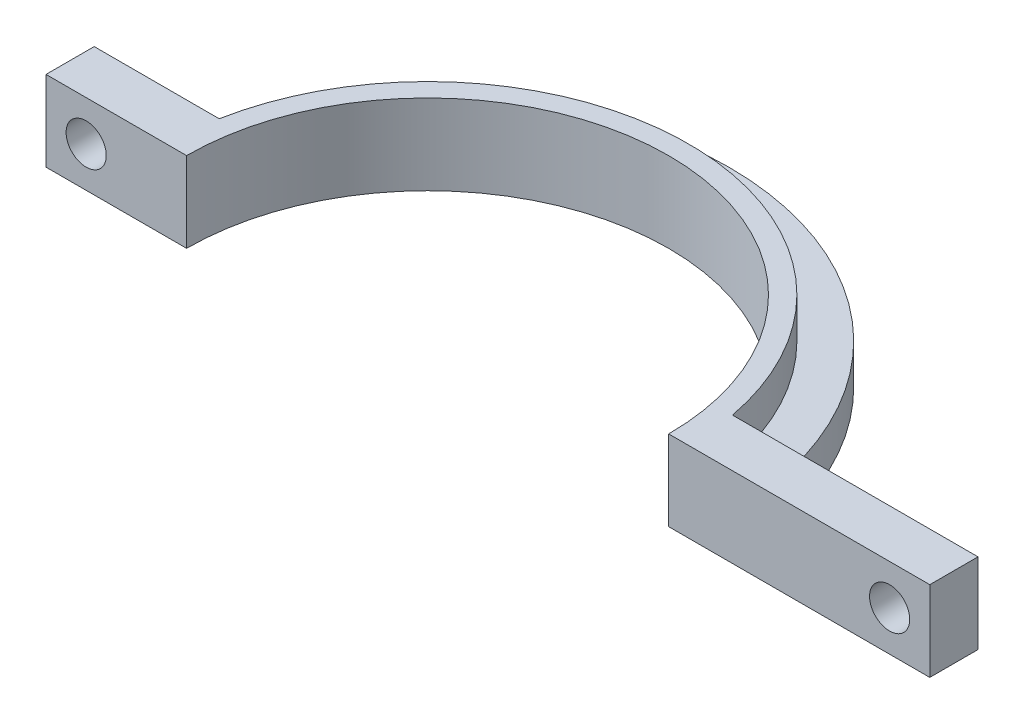
SolidWorks part; units mm, degrees
ref_plane "Front Plane" through (0, 0, 0) normal (0, 0, 1) x (1, 0, 0)
ref_plane "Top Plane" through (0, 0, 0) normal (0, 1, 0) x (1, 0, 0)
ref_plane "Right Plane" through (0, 0, 0) normal (1, 0, 0) x (0, 0, -1)
sketch "Sketch1" plane through (0, 0, 0) normal (0, 1, 0) x (1, 0, 0)
  line L2 (0, 30) -> (0, -30) construction
  line L3 (32.5, 0) -> (62.5, 0)
  line L4 (62.5, 0) -> (62.5, 6)
  line L5 (-32.5, 0) -> (-62.5, 0)
  line L6 (-62.5, 0) -> (-62.5, 6)
  line L7 (62.5, 6) -> (31.9414, 6)
  line L8 (-47.5, 6) -> (-47.5, 0)
  line L11 (-30, 0) -> (-32.5, 0)
  line L12 (30, 0) -> (32.5, 0)
  line L13 (-62.5, 6) -> (-31.9414, 6)
  circle A0 centre (0, 0) radius 30
  circle A3 centre (0, 0) radius 32.5
  dimension "D1" = 60
  dimension "D2" = 65
  dimension "D4" = 6
  dimension "D3" = 30
  dimension "D5" = 15
extrude "Boss-Extrude1" add sketch "Sketch1" along normal blind 10
sketch "Sketch3" plane through (0, 0, 0) normal (0, 0, 1) x (1, 0, 0)
  line L0 (-47.5, 5) -> (-42.5, 5) construction
  line L2 (62.5, 5) -> (57.5, 5) construction
  line L3 (-47.5, 10) -> (-47.5, 0) construction
  line L4 (62.5, 10) -> (62.5, 0) construction
  circle A5 centre (57.5, 5) radius 2.5
  circle A6 centre (-42.5, 5) radius 2.5
  dimension "D1" = 5
  dimension "D2" = 5
extrude "Cut-Extrude1" cut sketch "Sketch3" against normal blind 10
sketch "Sketch5" plane through (0, 0, 0) normal (0, 1, 0) x (1, 0, 0)
  line L0 (-37.5, 0) -> (-32.5, 0)
  line L1 (32.5, 0) -> (37.5, 0)
  circle A0 centre (0, 0) radius 37.5
  circle A1 centre (0, 0) radius 32.5
  dimension "D1" = 75
  dimension "D2" = 65
extrude "Boss-Extrude2" add sketch "Sketch5" along normal blind 5 contours A1 L1 A0 L0
sketch "Sketch9" plane through (0, 0, 0) normal (0, -1, 0) x (1, 0, 0)
  line L0 (-34.8065, -10) -> (-28.2843, -10)
  line L1 (-34.8065, -13.9556) -> (-28.2843, -13.9556)
  line L2 (0, 0) -> (0, -30) construction
  line L5 (-34.8065, -13.9556) -> (-34.8065, -10)
  line L6 (-28.2843, -10) -> (-28.2843, -13.9556)
  line L7 (34.8065, -13.9556) -> (28.2843, -13.9556)
  line L8 (34.8065, -13.9556) -> (34.8065, -10)
  line L9 (34.8065, -10) -> (28.2843, -10)
  line L10 (28.2843, -10) -> (28.2843, -13.9556)
  arc A0 (-30, 0) -> (30, 0) centre (0, 0) ccw construction
  arc A1 (-37.0169, -6) -> (37.0169, -6) centre (0, 0) ccw construction
  dimension "D2" = 3.9556
  dimension "D1" = 6.5222
